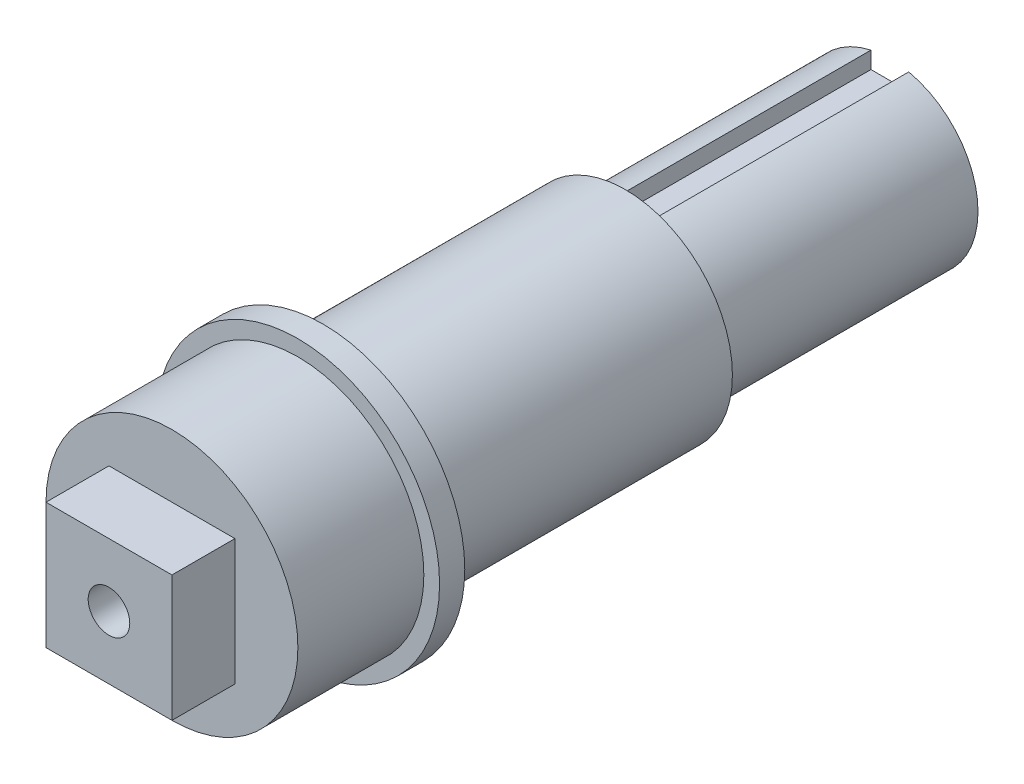
SolidWorks part; units mm, degrees
material "Plain Carbon Steel"
ref_plane "Front Plane" through (0, 0, 0) normal (0, 0, 1) x (1, 0, 0)
ref_plane "Top Plane" through (0, 0, 0) normal (0, 1, 0) x (1, 0, 0)
ref_plane "Right Plane" through (0, 0, 0) normal (1, 0, 0) x (0, 0, -1)
sketch "Sketch1" plane through (0, 0, 0) normal (0, 0, 1) x (1, 0, 0)
  circle A0 centre (0, 0) radius 7
  dimension "D1" = 14
extrude "Boss-Extrude1" add sketch "Sketch1" along normal blind 21
sketch "Sketch3" plane through (0, 0, 0) normal (0, 0, -1) x (-1, 0, 0)
  line L0 (0, 55) -> (0, -55) construction
  line L1 (-1.5, 5.5) -> (1.5, 5.5)
  line L2 (-1.5, 5.5) -> (-1.5, 8.5)
  line L3 (-1.5, 8.5) -> (1.5, 8.5)
  line L4 (1.5, 5.5) -> (1.5, 8.5)
  line L5 (-1.5, 5.5) -> (1.5, 8.5) construction
  line L6 (-1.5, 8.5) -> (1.5, 5.5) construction
  circle A0 centre (0, 0) radius 7 construction
  point P0 (0, 7)
  dimension "D1" = 1.5
  dimension "D2" = 3
extrude "Cut-Extrude1" cut sketch "Sketch3" against normal blind 21
sketch "Sketch6" plane through (0, 0, 21) normal (0, 0, 1) x (1, 0, 0)
  circle A0 centre (0, 0) radius 8.5
  dimension "D1" = 17
extrude "Boss-Extrude2" add sketch "Sketch6" along normal blind 24
sketch "Sketch7" plane through (0, 0, 45) normal (0, 0, 1) x (1, 0, 0)
  circle A0 centre (0, 0) radius 10
  dimension "D1" = 20
extrude "Boss-Extrude3" add sketch "Sketch7" along normal blind 17
fillet "Fillet1" radius 0.6 1 edges at (8.5, 0, 45)
ref_plane "Plane1" through (0, 0, 45) normal (0, 0, -1) x (-1, 0, 0)
sketch "Sketch8" plane through (0, 0, 45) normal (0, 0, -1) x (-1, 0, 0)
  circle A0 centre (0, 0) radius 11.25
  dimension "D1" = 22.5
extrude "Boss-Extrude4" add sketch "Sketch8" against normal blind 2
ref_plane "Plane2" through (0, 0, 57) normal (0, 0, 1) x (1, 0, 0)
sketch "Sketch10" plane through (0, 0, 57) normal (0, 0, 1) x (1, 0, 0)
  line L1 (-5, -5) -> (5, -5)
  line L2 (-5, -5) -> (-5, 5)
  line L3 (-5, 5) -> (5, 5)
  line L4 (5, -5) -> (5, 5)
  line L5 (-5, -5) -> (5, 5) construction
  line L6 (-5, 5) -> (5, -5) construction
  circle A1 centre (0, 0) radius 11
  point P0 (0, 0)
  dimension "D1" = 22
  dimension "D2" = 10
extrude "Cut-Extrude2" cut sketch "Sketch10" along normal up to surface (5 mm away) contours L2 A1 | L3 A1 | L4 A1 | L1 A1
hole_wizard "M4x0.7 Tapped Hole1" positions "Sketch11" profile "Sketch12" tap size "M4x0.7" standard "ANSI Metric"
sketch "Sketch11" plane through (0, 0, 62) normal (0, 0, 1) x (1, 0, 0)
  point P0 (0, 0)
sketch "Sketch12" plane through (0, 0, 62) normal (1, 0, 0) x (0, -1, 0)
  line L0 (0, 0) -> (0, 20.9914)
  line L1 (0, 20.9914) -> (1.65, 20)
  line L2 (1.65, 20) -> (1.65, 0)
  line L5 (1.65, 0) -> (0, 0)
  line L10 (0, 20.9914) -> (-1.65, 20) construction
  line L11 (0, -6.35) -> (0, 107.95) construction
  dimension "Tap Drill Dia." = 3.3
  dimension "Tap Drill Depth" = 20
  dimension "Drill Angle" = 118
